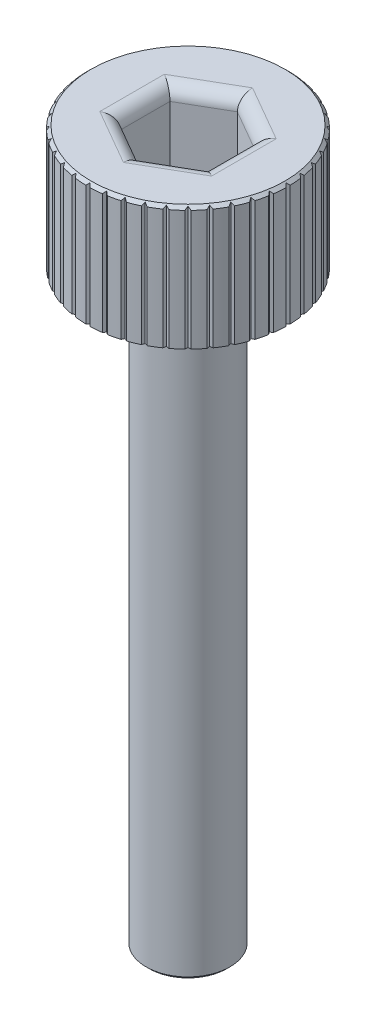
SolidWorks part; units mm, degrees
material "1060 Alloy"
ref_plane "Front Plane" through (0, 0, 0) normal (0, 0, 1) x (1, 0, 0)
ref_plane "Top Plane" through (0, 0, 0) normal (0, 1, 0) x (1, 0, 0)
ref_plane "Right Plane" through (0, 0, 0) normal (1, 0, 0) x (0, 0, -1)
sketch "Sketch1" plane through (0, 0, 0) normal (0, 0, 1) x (1, 0, 0)
  line L0 (0, 0) -> (0, 41.1734)
  line L1 (0, 41.1734) -> (5.6116, 41.1734)
  line L2 (5.7912, 40.9938) -> (5.7912, 34.036)
  line L3 (5.7912, 34.036) -> (2.4257, 34.036)
  line L4 (2.4257, 34.036) -> (2.4257, 0.1796)
  line L5 (2.2461, 0) -> (0, 0)
  line L6 (5.6116, 41.1734) -> (5.7912, 40.9938)
  line L7 (2.2461, 0) -> (2.4257, 0.1796)
  dimension "D1" = 5.7912
  dimension "D2" = 2.4257
  dimension "D3" = 41.1734
  dimension "D4" = 7.1374
  dimension "D5" = 45
  dimension "D6" = 0.254
  dimension "D7" = 45
  dimension "D8" = 0.254
revolve "Revolve1" add sketch "Sketch1" angle 360 about L0
sketch "Sketch2" plane through (0, 41.1734, 0) normal (0, 1, 0) x (1, 0, 0)
  line L1 (0, -2.8575) -> (2.4747, -1.4287)
  line L2 (2.4747, -1.4287) -> (2.4747, 1.4288)
  line L3 (2.4747, 1.4288) -> (0, 2.8575)
  line L4 (0, 2.8575) -> (-2.4747, 1.4288)
  line L5 (-2.4747, 1.4288) -> (-2.4747, -1.4287)
  line L6 (-2.4747, -1.4287) -> (0, -2.8575)
  circle A0 centre (0, 0) radius 2.4747 construction
  dimension "D1" = 5.715
extrude "Cut-Extrude1" cut sketch "Sketch2" against normal blind 4.064
fillet "Fillet1" radius 0.762 6 edges at (-2.4747, 41.1734, 0) (-1.2373, 41.1734, 2.1431) (1.2373, 41.1734, 2.1431) (2.4747, 41.1734, 0) (1.2373, 41.1734, -2.1431) (-1.2373, 41.1734, -2.1431)
sketch "Sketch3" plane through (0, 41.1734, 0) normal (0, 1, 0) x (1, 0, 0)
  line L3 (0, 0) -> (0, 9.3963) construction
  line L4 (0, 5.6642) -> (-2.032, 7.6962)
  line L5 (0, 5.6642) -> (2.032, 7.6962)
  line L6 (-2.032, 7.6962) -> (2.032, 7.6962)
  dimension "D1" = 90
  dimension "D2" = 5.6642
  dimension "D3" = 2.032
  dimension "D4" = 2.032
extrude "Cut-Extrude3" cut sketch "Sketch3" against normal blind 9.144
pattern_circular "CirPattern1" count 40 over 360 about axis through (0, 0, 0) along (0, 1, 0) of "Cut-Extrude3"
